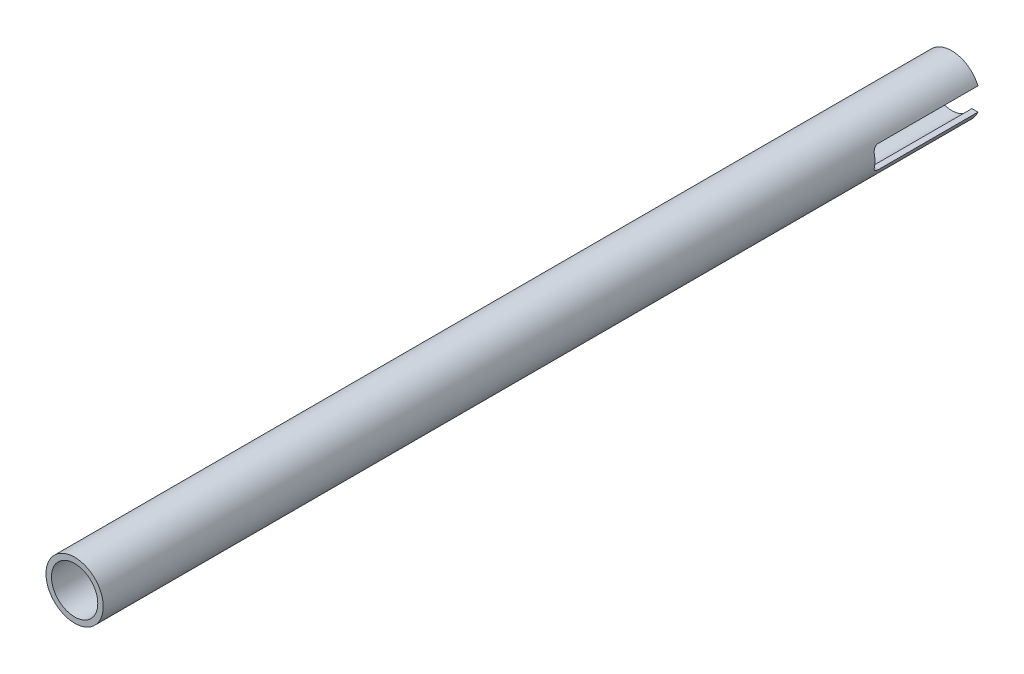
SolidWorks part; units mm, degrees
material "AISI 4130 Steel, annealed at 865C"
ref_plane "Front Plane" through (0, 0, 0) normal (0, 0, 1) x (1, 0, 0)
ref_plane "Top Plane" through (0, 0, 0) normal (0, 1, 0) x (1, 0, 0)
ref_plane "Right Plane" through (0, 0, 0) normal (1, 0, 0) x (0, 0, -1)
sketch "Sketch1" plane through (0, 0, 0) normal (0, 0, 1) x (1, 0, 0)
  circle A0 centre (0, 0) radius 6.477
  circle A1 centre (0, 0) radius 8.001
  dimension "D1" = 12.954
  dimension "D2" = 16.002
extrude "Boss-Extrude1" add sketch "Sketch1" along normal blind 245.11
sketch "Sketch2" plane through (0, 0, 0) normal (1, 0, 0) x (0, 0, -1)
  line L0 (0, 3.175) -> (-27.94, 3.175)
  line L1 (0, 8.8011) -> (0, -8.8011) construction
  line L2 (-27.94, -3.175) -> (0, -3.175)
  line L3 (-29.464, 1.651) -> (-29.464, -1.651)
  line L4 (0, -8.001) -> (0, 8.001) construction
  arc A0 (-29.464, 1.651) -> (-27.94, 3.175) centre (-27.94, 1.651) cw
  arc A1 (-27.94, -3.175) -> (-29.464, -1.651) centre (-27.94, -1.651) cw
  dimension "D5" = 27.94
  dimension "D6" = 29.464
  dimension "D1" = 29.464
  dimension "D2" = 27.94
  dimension "D3" = 6.35
  dimension "D4" = 3.175
extrude "Cut-Extrude1" cut sketch "Sketch2" against normal through all both and the other way through all
